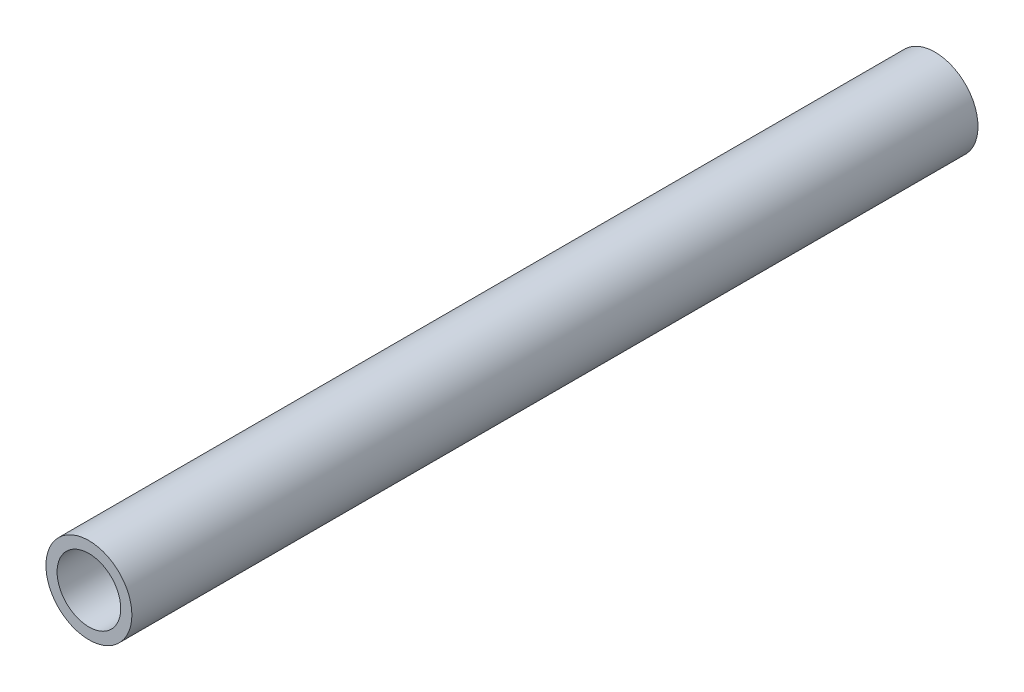
SolidWorks part; units mm, degrees
ref_plane "Front Plane" through (0, 0, 0) normal (0, 0, 1) x (1, 0, 0)
ref_plane "Top Plane" through (0, 0, 0) normal (0, 1, 0) x (1, 0, 0)
ref_plane "Right Plane" through (0, 0, 0) normal (1, 0, 0) x (0, 0, -1)
sketch "Sketch1" plane through (0, 0, 0) normal (0, 0, 1) x (1, 0, 0)
  circle A0 centre (0, 0) radius 10.668
  dimension "Pipe OD" = 21.336
extrude "Extrude-Thin1" add sketch "Sketch1" along normal mid plane 210 thin thin type one direction reverse wall 2.7686
